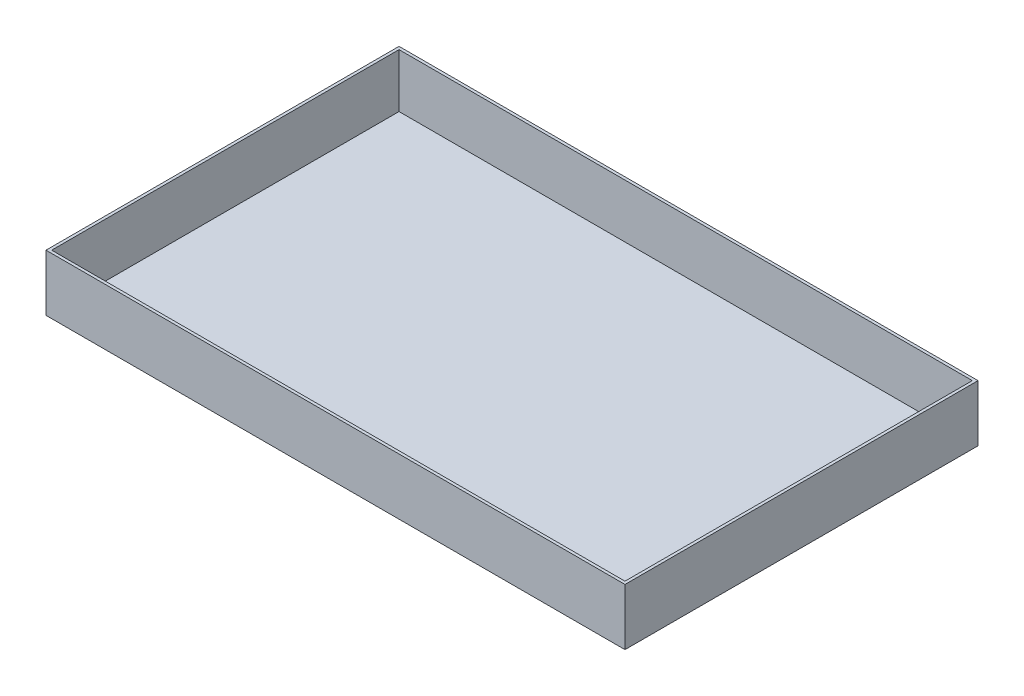
SolidWorks part; units mm, degrees
ref_plane "前视基准面" through (0, 0, 0) normal (0, 0, 1) x (1, 0, 0)
ref_plane "上视基准面" through (0, 0, 0) normal (0, 1, 0) x (1, 0, 0)
ref_plane "右视基准面" through (0, 0, 0) normal (1, 0, 0) x (0, 0, -1)
sketch "草图1" plane through (0, 0, 0) normal (0, 1, 0) x (1, 0, 0)
  line L1 (0, 0) -> (410, 0)
  line L2 (0, 0) -> (0, 250)
  line L3 (0, 250) -> (410, 250)
  line L4 (410, 0) -> (410, 250)
  dimension "D1" = 410
  dimension "D2" = 250
extrude "凸台-拉伸1" add sketch "草图1" along normal blind 40
shell "抽壳1" thickness 2
